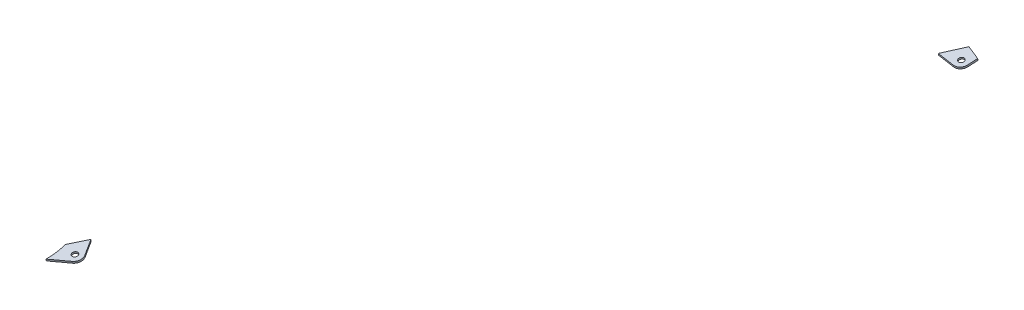
SolidWorks part; units mm, degrees
material "Stal węglowa"
ref_plane "Płaszczyzna XY" through (0, 0, 0) normal (0, 0, 1) x (1, 0, 0)
ref_plane "Płaszczyzna XZ" through (0, 0, 0) normal (0, 1, 0) x (1, 0, 0)
ref_plane "Płaszczyzna YZ" through (0, 0, 0) normal (1, 0, 0) x (0, 0, -1)
sketch "Szkic1" plane through (0, 358.0927, 69.6062) normal (0, -0.9816, -0.1908) x (-1, 0, 0)
  line L0 (-1362.9238, -419.8541) -> (-1364.1826, -410.0795)
  line L1 (-1353.9675, -426.7668) -> (-1335.1353, -424.3415)
  line L2 (-952.8484, -984.8258) -> (-944.1688, -969.3431)
  line L3 (-949.7821, -995.7161) -> (-931.2534, -1006.1032)
  circle A1 centre (-945.8701, -988.7378) radius 3
  arc A2 (-952.8484, -984.8258) -> (-949.7821, -995.7161) centre (-945.8701, -988.7378) ccw
  circle A4 centre (-1354.9893, -418.8323) radius 3
  arc A5 (-1362.9238, -419.8541) -> (-1353.9675, -426.7668) centre (-1354.9893, -418.8323) ccw
  circle A6 centre (-945.8701, -988.7378) radius 8 construction
  circle A7 centre (-1354.9893, -418.8323) radius 8 construction
  spline S2 degree 3 poles (-932.0709, -985.2692) (-936.1017, -979.9629) (-940.1343, -974.6542) (-944.1688, -969.3431) knots 0 0 0 0 0.028373 0.028373 0.028373 0.028373 weights 1 0.999984 0.999969 0.999955
  spline S3 degree 3 poles (-1335.1353, -424.3415) (-1339.8577, -417.7687) (-1344.582, -411.1933) (-1349.3081, -404.6153) knots 0.966452 0.966452 0.966452 0.966452 1 1 1 1 weights 0.999947 0.999964 0.999982 1
  spline S7 degree 3 poles (-931.2534, -1006.1032) (-931.3469, -1005.7079) (-931.4339, -1005.3107) (-931.7308, -1003.8511) (-931.9049, -1002.7742) (-932.3178, -999.5504) (-932.4509, -997.4056) (-932.5265, -993.1219) (-932.4679, -990.983) (-932.2713, -987.6533) (-932.1797, -986.461) (-932.0709, -985.2692) knots 0.038995 0.038995 0.038995 0.038995 0.0625 0.0625 0.125 0.125 0.25 0.25 0.375 0.375 0.444789 0.444789 0.444789 0.444789
  spline S10 degree 3 poles (-1349.3081, -404.6153) (-1354.3271, -406.5307) (-1359.3052, -408.3557) (-1364.1826, -410.0795) knots 0.918492 0.918492 0.918492 0.918492 1 1 1 1 weights 0.85094 0.896218 0.945904 1
  dimension "D3" = 90
  dimension "D4" = 90
  dimension "D2" = 5
extrude "Dodanie-wyciągnięcie1" add sketch "Szkic1" along normal blind 2
